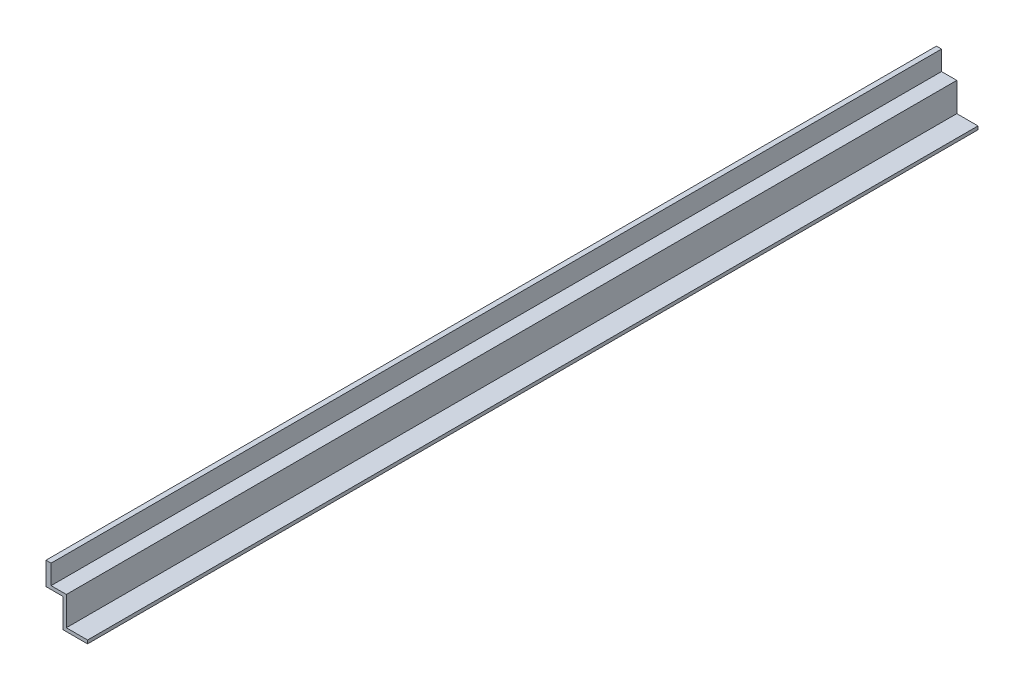
SolidWorks part; units mm, degrees
material "1.4000 (X6Cr13)"
ref_plane "Alzado" through (0, 0, 0) normal (0, 0, 1) x (1, 0, 0)
ref_plane "Planta" through (0, 0, 0) normal (0, 1, 0) x (1, 0, 0)
ref_plane "Vista lateral" through (0, 0, 0) normal (1, 0, 0) x (0, 0, -1)
sketch "Croquis1" plane through (0, 0, 0) normal (0, 1, 0) x (1, 0, 0)
  line L1 (0, 0) -> (6, 0)
  line L2 (0, 0) -> (0, -1050)
  line L3 (0, -1050) -> (6, -1050)
  line L4 (6, 0) -> (6, -1050)
  dimension "D1" = 1050
  dimension "D2" = 6
extrude "Saliente-Extruir1" add sketch "Croquis1" against normal blind 23
sketch "Croquis2" plane through (0, 0, 1050) normal (0, 0, 1) x (1, 0, 0)
  line L0 (6, -23) -> (6, 0) construction
  line L1 (0, -23) -> (24, -23)
  line L2 (0, -23) -> (0, -27)
  line L3 (0, -27) -> (24, -27)
  line L4 (24, -23) -> (24, -27)
  dimension "D1" = 18
  dimension "D2" = 4
extrude "Saliente-Extruir2" add sketch "Croquis2" against normal blind 1050
sketch "Croquis3" plane through (0, 0, 1050) normal (0, 0, 1) x (1, 0, 0)
  line L1 (24, -27) -> (20, -27)
  line L2 (24, -27) -> (24, -57)
  line L3 (24, -57) -> (20, -57)
  line L4 (20, -27) -> (20, -57)
  dimension "D1" = 4
  dimension "D2" = 34
extrude "Saliente-Extruir3" add sketch "Croquis3" against normal blind 1050
sketch "Croquis4" plane through (0, 0, 1050) normal (0, 0, 1) x (1, 0, 0)
  line L1 (20, -57) -> (49, -57)
  line L2 (20, -57) -> (20, -61)
  line L3 (20, -61) -> (49, -61)
  line L4 (49, -57) -> (49, -61)
  dimension "D1" = 29
  dimension "D2" = 4
extrude "Saliente-Extruir4" add sketch "Croquis4" against normal blind 1050
